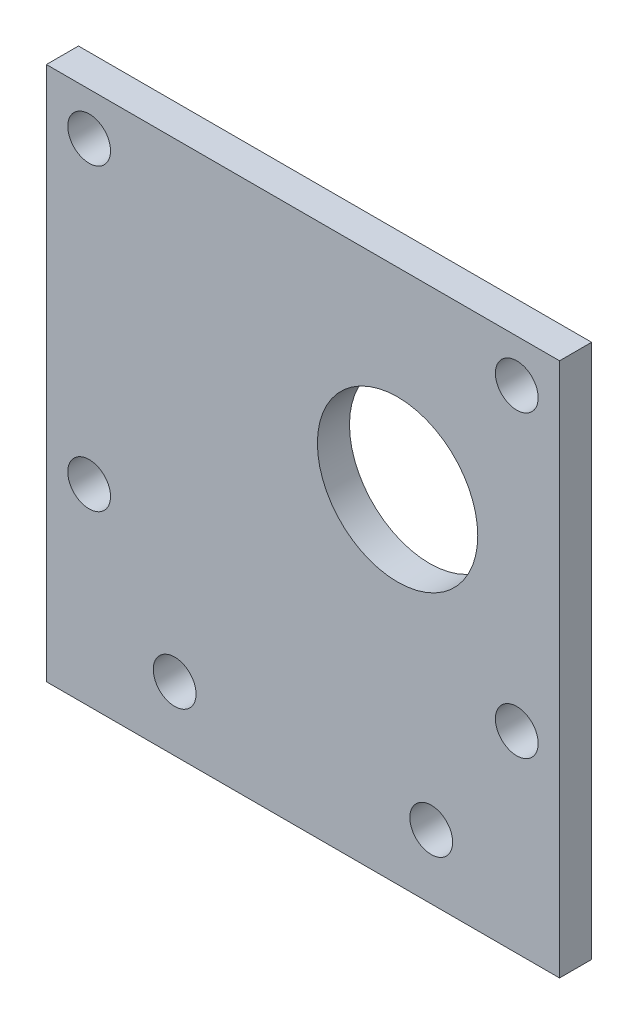
SolidWorks part; units mm, degrees
ref_plane "Front Plane" through (0, 0, 0) normal (0, 0, 1) x (1, 0, 0)
ref_plane "Top Plane" through (0, 0, 0) normal (0, 1, 0) x (1, 0, 0)
ref_plane "Right Plane" through (0, 0, 0) normal (1, 0, 0) x (0, 0, -1)
sketch "Sketch2" plane through (0, 0, 0) normal (0, 0, 1) x (1, 0, 0)
  line L0 (24, 50) -> (24, 0) construction
  line L1 (0, 0) -> (48, 0)
  line L2 (0, 0) -> (0, 50)
  line L3 (0, 50) -> (48, 50)
  line L4 (48, 0) -> (48, 50)
  circle A0 centre (4, 46) radius 2
  circle A1 centre (44, 46) radius 2
  circle A2 centre (44, 18) radius 2
  circle A3 centre (4, 18) radius 2
  circle A4 centre (32.85, 32) radius 7.5
  circle A5 centre (12, 6) radius 2
  circle A6 centre (36, 6) radius 2
  dimension "D3" = 4
  dimension "D8" = 15
  dimension "D11" = 4
  dimension "D12" = 4
  dimension "D1" = 48
  dimension "D2" = 50
  dimension "D4" = 20
  dimension "D5" = 20
  dimension "D6" = 28
  dimension "D7" = 28.85
  dimension "D9" = 14
  dimension "D10" = 4
  dimension "D13" = 12
  dimension "D14" = 12
  dimension "D15" = 6
  dimension "D16" = 6
extrude "Boss-Extrude2" add sketch "Sketch2" along normal blind 3
